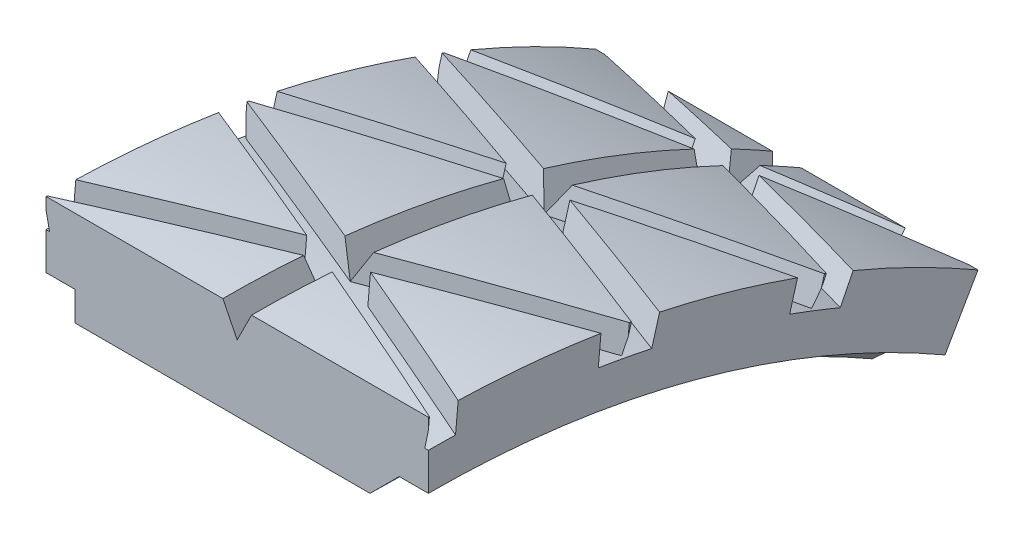
SolidWorks part; units mm, degrees
ref_plane "Front Plane" through (0, 0, 0) normal (0, 0, 1) x (1, 0, 0)
ref_plane "Top Plane" through (0, 0, 0) normal (0, 1, 0) x (1, 0, 0)
ref_plane "Right Plane" through (0, 0, 0) normal (1, 0, 0) x (0, 0, -1)
sketch "Sketch1" plane through (0, 0, 0) normal (0, 0, 1) x (1, 0, 0)
  line L0 (-20, 115) -> (20, 115)
  line L1 (-20, 115) -> (-20, 108.1)
  line L2 (-20, 108.1) -> (-16.95, 108.1)
  line L3 (-16.95, 108.1) -> (-16.95, 105.05)
  line L4 (-16.95, 105.05) -> (13.9, 105.05)
  line L5 (13.9, 105.05) -> (16.95, 108.1)
  line L6 (16.95, 108.1) -> (20, 108.1)
  line L7 (20, 108.1) -> (20, 115)
  point P2 (0, 115)
  dimension "D2" = 3.05
  dimension "D1" = 20
  dimension "D3" = 3.05
  dimension "D4" = 3.05
  dimension "D5" = 3.05
  dimension "D6" = 115
  dimension "D7" = 3.05
  dimension "D8" = 105.05
ref_axis "Axis1" through (22, 0, 0) along (-1, 0, 0)
revolve "Revolve1" add sketch "Sketch1" angle 360 about axis through (22, 0, 0) along (-1, 0, 0)
sketch "Sketch2" plane through (0, 0, 0) normal (0, 0, 1) x (1, 0, 0)
  line L0 (-20, 112) -> (20, 112)
  dimension "D1" = 112
surface "Surface-Revolve1" sketch "Sketch2" parameters "D1"=360
ref_plane "Plane1" through (0, 0, 117) normal (0, 0, 1) x (1, 0, 0)
sketch "Sketch3" plane through (0, 0, 117) normal (0, 0, 1) x (1, 0, 0)
  line L0 (-20, 7.5) -> (-3.3333, 0)
  line L1 (-20, -112) -> (-20, 112) construction
  line L2 (20, -115) -> (20, 115) construction
  line L3 (20, -10.5) -> (20, -7.5)
  line L4 (20, -7.5) -> (3.3333, 0)
  line L5 (-20, 10.5) -> (-20, 7.5)
  line L6 (20, 7.5) -> (3.3333, 0)
  line L7 (-20, -10.5) -> (-20, -7.5)
  line L8 (-20, 115) -> (-20, -115) construction
  line L9 (-20, -7.5) -> (-3.3333, 0)
  line L10 (20, 10.5) -> (20, 7.5)
  line L11 (0, 1.5) -> (-20, 10.5)
  line L12 (0, -1.5) -> (20, -10.5)
  line L13 (0, 1.5) -> (20, 10.5)
  line L14 (0, -1.5) -> (-20, -10.5)
  dimension "D1" = 3
  dimension "D2" = 3
  dimension "D3" = 15
  dimension "D4" = 15
  dimension "D5" = 7.5
extrude "Cut-Extrude1" cut sketch "Sketch3" against normal up to surface (5.01 mm away)
pattern_circular "CirPattern1" count 34 over 360 about axis through (0, 0, 0) along (1, 0, 0) of "Cut-Extrude1"
sketch "Sketch4" plane through (0, 0, 0) normal (0, 0, 1) x (1, 0, 0)
  line L0 (20, 115) -> (-20, 115) construction
  line L3 (-1.5, 115) -> (1.5, 115)
  line L5 (-0.5, 113) -> (1.5, 115) construction
  line L6 (-1.5, 115) -> (0.5, 113) construction
  line L7 (-1.5, 115) -> (0, 112)
  line L8 (0, 112) -> (1.5, 115)
  point P0 (0, 113.5)
  dimension "D1" = 115
  dimension "D2" = 3
  dimension "D3" = 3
  dimension "D4" = 1.5
revolve "Cut-Revolve1" cut sketch "Sketch4" angle 360 about axis through (22, 0, 0) along (-1, 0, 0)
sketch "Sketch5" plane through (-20, 0, 0) normal (-1, 0, 0) x (0, 0, 1)
  line L0 (0, 0) -> (0, 124.8803)
  line L1 (0, 0) -> (-66.7379, 115.5934)
  arc A0 (0, 124.8803) -> (-66.7379, 115.5934) centre (-19.655, 21.6854) ccw
  circle A1 centre (0, 0) radius 105.05 construction
  dimension "D1" = 30
extrude "Cut-Extrude2" cut sketch "Sketch5" against normal through all flip side to cut
delete or keep bodies "Body-Delete/Keep 1" type delete bodies bodies 102
